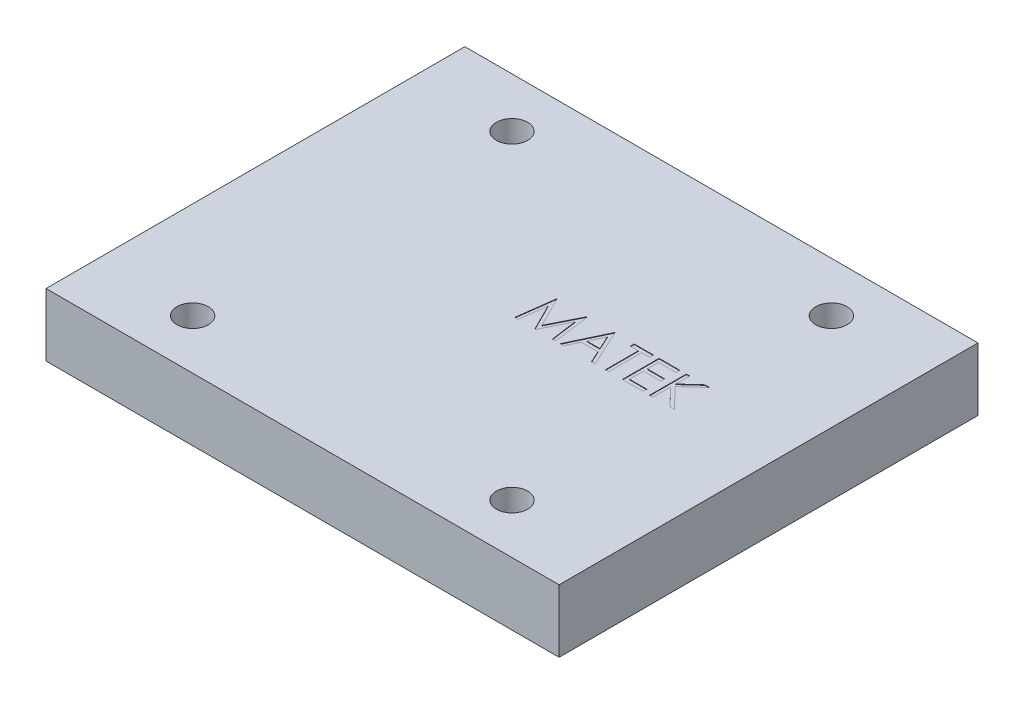
SolidWorks part; units mm, degrees
ref_plane "Front Plane" through (0, 0, 0) normal (0, 0, 1) x (1, 0, 0)
ref_plane "Top Plane" through (0, 0, 0) normal (0, 1, 0) x (1, 0, 0)
ref_plane "Right Plane" through (0, 0, 0) normal (1, 0, 0) x (0, 0, -1)
sketch "Sketch1" plane through (0, 0, 0) normal (0, 1, 0) x (1, 0, 0)
  line L1 (24.5, 20) -> (-24.5, 20)
  line L2 (24.5, 20) -> (24.5, -20)
  line L3 (24.5, -20) -> (-24.5, -20)
  line L4 (-24.5, 20) -> (-24.5, -20)
  line L5 (24.5, 20) -> (-24.5, -20) construction
  line L6 (24.5, -20) -> (-24.5, 20) construction
  circle A0 centre (-15.25, 15.25) radius 1.5
  circle A1 centre (15.25, 15.25) radius 1.5
  circle A2 centre (15.25, -15.25) radius 1.5
  circle A3 centre (-15.25, -15.25) radius 1.5
  point P0 (0, 0)
  dimension "D2" = 3
  dimension "D1" = 40
  dimension "59" = 49
  dimension "D5" = 15.25
  dimension "D6" = 15.25
  dimension "D3" = 2
  dimension "D4" = 2
extrude "Boss-Extrude1" add sketch "Sketch1" along normal blind 6
sketch "Sketch2" plane through (0, 6, 0) normal (0, 1, 0) x (1, 0, 0)
  text T0 "MATEK"
extrude "Cut-Extrude1" cut sketch "Sketch2" against normal blind 0.05
